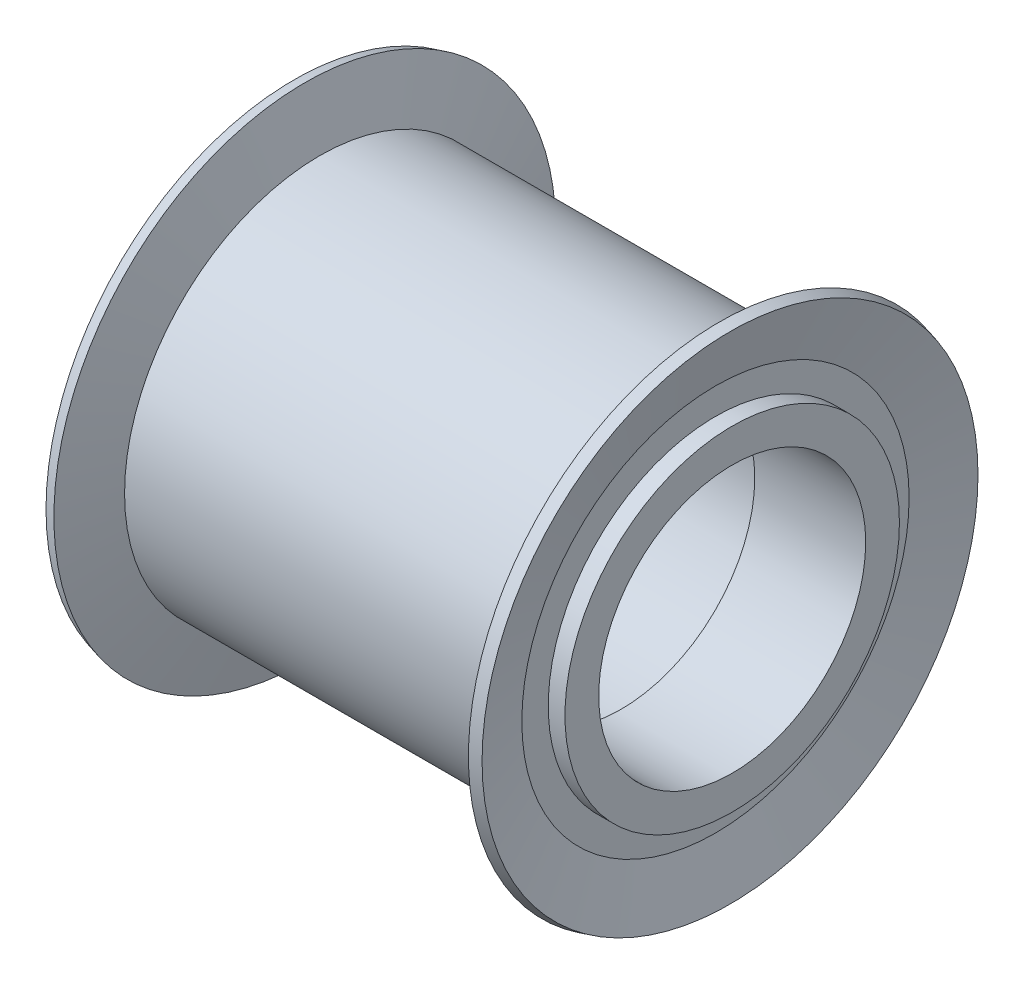
SolidWorks part; units mm, degrees
ref_plane "Front Plane" through (0, 0, 0) normal (0, 0, 1) x (1, 0, 0)
ref_plane "Top Plane" through (0, 0, 0) normal (0, 1, 0) x (1, 0, 0)
ref_plane "Right Plane" through (0, 0, 0) normal (1, 0, 0) x (0, 0, -1)
sketch "Sketch1" plane through (0, 0, 0) normal (0, 0, 1) x (1, 0, 0)
  line L0 (-4.1304, 6.5217) -> (-4.7826, 6.5217)
  line L1 (-4.7826, 6.5217) -> (-4.7826, 5.6522)
  line L2 (3.8043, 7.6087) -> (3.8043, 0) construction
  line L3 (8.0643, 5.6522) -> (8.0643, 5.2066)
  line L4 (4.0643, 5.6522) -> (8.0643, 5.6522)
  line L9 (12.3913, 5.2066) -> (12.3913, 6.5217)
  line L10 (12.3913, 6.5217) -> (11.7391, 6.5217)
  line L11 (11.7391, 6.5217) -> (11.7391, 7.5515)
  line L12 (11.7391, 7.5515) -> (12.3068, 9.6701)
  line L13 (12.3068, 9.6701) -> (11.8868, 9.7826)
  line L14 (11.8868, 9.7826) -> (11.3043, 7.6087)
  line L15 (11.3043, 7.6087) -> (-3.6957, 7.6087)
  line L16 (-3.6957, 7.6087) -> (-4.2782, 9.7826)
  line L17 (-4.2782, 9.7826) -> (-4.6981, 9.6701)
  line L18 (-4.6981, 9.6701) -> (-4.1304, 7.5515)
  line L19 (-4.1304, 7.5515) -> (-4.1304, 6.5217)
  line L20 (-4.7848, 0) -> (4.7848, 0) construction
  line L21 (4.0643, 5.6522) -> (4.0643, 5.913)
  line L22 (4.0643, 5.913) -> (3.5443, 5.913)
  line L23 (3.5443, 5.913) -> (3.5443, 5.6522)
  line L24 (3.5443, 5.6522) -> (-4.7826, 5.6522)
  line L25 (8.0643, 5.2066) -> (12.3913, 5.2066)
  point P22 (3.8043, 5.913)
  dimension "D1" = 0.52
  dimension "D2" = 15
  dimension "D3" = 0.4348
  dimension "D4" = 1.087
  dimension "D5" = 4
revolve "Revolve1" add sketch "Sketch1" angle 360 about L20
